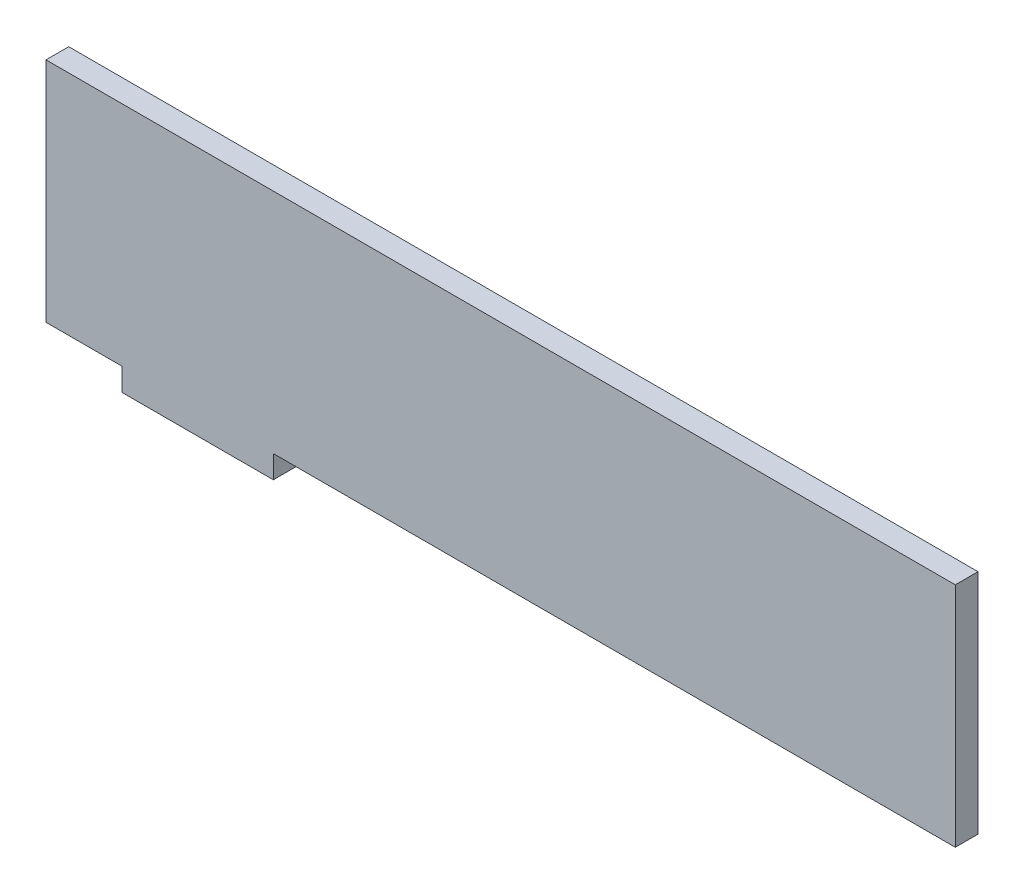
SolidWorks part; units mm, degrees
ref_plane "Front Plane" through (0, 0, 0) normal (0, 0, 1) x (1, 0, 0)
ref_plane "Top Plane" through (0, 0, 0) normal (0, 1, 0) x (1, 0, 0)
ref_plane "Right Plane" through (0, 0, 0) normal (1, 0, 0) x (0, 0, -1)
sketch "Sketch1" plane through (0, 0, 0) normal (0, 0, 1) x (1, 0, 0)
  line L0 (-25, -13) -> (-35, -13)
  line L1 (-35, -13) -> (-35, 17)
  line L2 (-35, 17) -> (85, 17)
  line L3 (85, 17) -> (85, -13)
  line L4 (85, -13) -> (-5, -13)
  line L5 (-5, -13) -> (-5, -16)
  line L6 (-5, -16) -> (-25, -16)
  line L7 (-25, -16) -> (-25, -13)
  dimension "D1" = 30
  dimension "D2" = 90
  dimension "D3" = 20
  dimension "D4" = 3
  dimension "D5" = 10
extrude "Boss-Extrude1" add sketch "Sketch1" along normal blind 3
